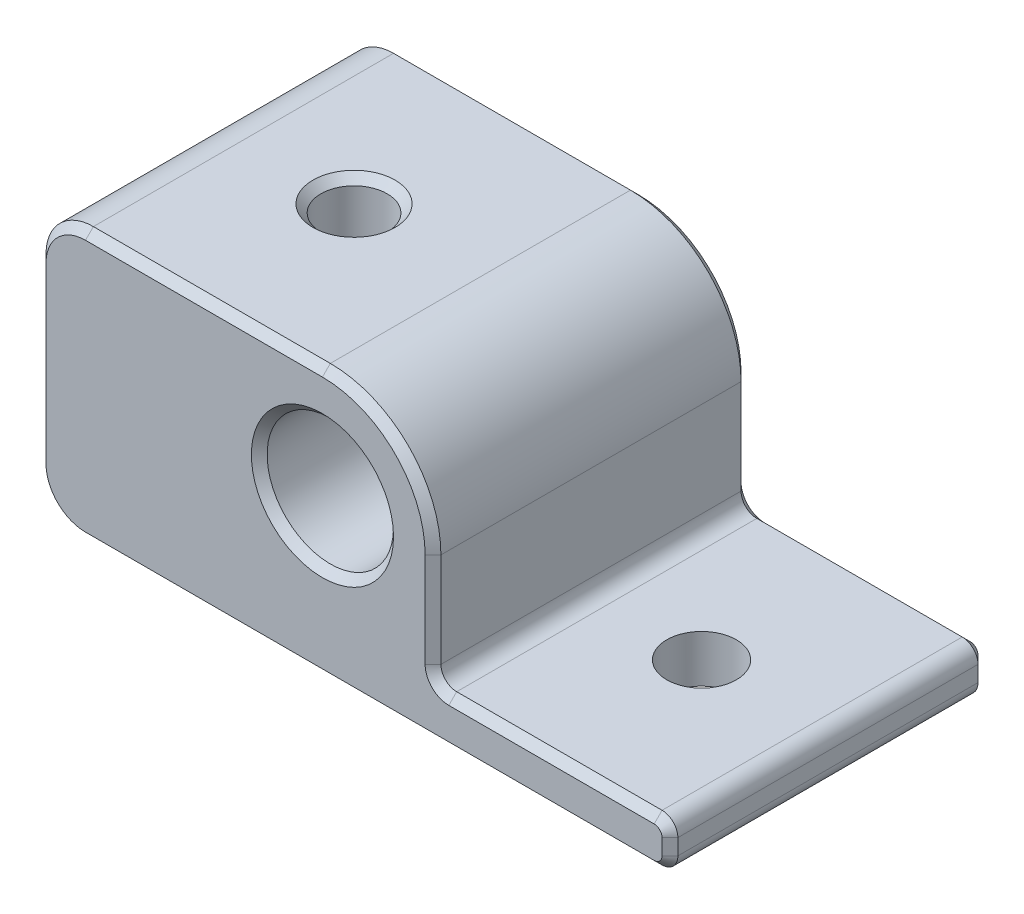
SolidWorks part; units mm, degrees
ref_plane "Front Plane" through (0, 0, 0) normal (0, 0, 1) x (1, 0, 0)
ref_plane "Top Plane" through (0, 0, 0) normal (0, 1, 0) x (1, 0, 0)
ref_plane "Right Plane" through (0, 0, 0) normal (1, 0, 0) x (0, 0, -1)
ref_plane "Plane1" through (0, -4.5711, 0) normal (0, -1, 0) x (1, 0, 0)
sketch "Sketch1" plane through (0, -4.5711, 0) normal (0, -1, 0) x (1, 0, 0)
  line L0 (19.5018, -0.4296) -> (59.5018, -0.4296)
  line L1 (59.5018, -0.4296) -> (59.5018, 19.5704)
  line L2 (59.5018, 19.5704) -> (19.5018, 19.5704)
  line L3 (19.5018, 19.5704) -> (19.5018, -0.4296)
extrude "Boss-Extrude1" add sketch "Sketch1" against normal blind 17
sketch "Sketch2" plane through (0, 0, 19.5704) normal (0, 0, 1) x (1, 0, 0)
  line L0 (44.5018, 12.4289) -> (44.5018, -1.5711)
  line L1 (44.5018, -1.5711) -> (59.5018, -1.5711)
  line L2 (59.5018, -1.5711) -> (59.5018, 12.4289)
  line L3 (59.5018, 12.4289) -> (44.5018, 12.4289)
extrude "Cut-Extrude1" cut sketch "Sketch2" against normal through all
hole_wizard "Ø4.4 (4.4) Diameter Hole1" positions "Sketch4" profile "Sketch3" hole size "Ø4.4" standard "ANSI Metric"
sketch "Sketch4" plane through (0, -4.5711, 0) normal (0, -1, 0) x (-1, 0, 0)
  point P0 (-51.5018, -9.5704)
sketch "Sketch3" plane through (51.5018, -4.5711, 9.5704) normal (1, 0, 0) x (0, 0, -1)
  line L0 (0, 0) -> (0, 17)
  line L1 (0, 17) -> (2.2, 17)
  line L2 (2.2, 17) -> (2.2, 0)
  line L5 (2.2, 0) -> (0, 0)
  line L11 (0, -6.35) -> (0, 107.95) construction
  dimension "Thru Hole Dia." = 4.4
  dimension "Thru Hole Depth" = 17
hole_wizard "Ø4.2 (4.2) Diameter Hole1" positions "Sketch6" profile "Sketch5" hole size "Ø4.2" standard "ANSI Metric"
sketch "Sketch6" plane through (0, 12.4289, 0) normal (0, 1, 0) x (1, 0, 0)
  point P0 (29.5018, -9.5704)
sketch "Sketch5" plane through (29.5018, 12.4289, 9.5704) normal (1, 0, 0) x (0, 0, 1)
  line L0 (0, 0) -> (0, 17)
  line L1 (0, 17) -> (2.1, 17)
  line L2 (2.1, 17) -> (2.1, 0)
  line L5 (2.1, 0) -> (0, 0)
  line L11 (0, -6.35) -> (0, 107.95) construction
  dimension "Thru Hole Dia." = 4.2
  dimension "Thru Hole Depth" = 17
hole_wizard "Hole1" positions "Sketch8" profile "Sketch7" legacy
sketch "Sketch8" plane through (0, 0, 19.5704) normal (0, 0, 1) x (1, 0, 0)
  point P0 (37.5018, 5.4289)
sketch "Sketch7" plane through (37.5018, 5.4289, 19.5704) normal (1, 0, 0) x (0, -1, 0)
  line L0 (0, 0) -> (0, 20)
  line L1 (0, 20) -> (3, 20)
  line L2 (3, 20) -> (3, 19)
  line L3 (3, 19) -> (4, 18)
  line L4 (4, 18) -> (4, 0)
  line L5 (4, 0) -> (0, 0)
  line L6 (0, -6.13) -> (0, 109.2824) construction
  line L7 (-3, 19) -> (-4, 18) construction
  line L8 (0, 20) -> (-3, 20) construction
  dimension "Diameter" = 6
  dimension "Depth" = 20
  dimension "C-Drill Diameter" = 8
  dimension "C-Drill Depth" = 18
  dimension "C-Drill Angle" = 90
fillet "Fillet1" radius 1 3 edges at (44.5018, -1.5711, 9.5704) (59.5018, -1.5711, 9.5704) (59.5018, -4.5711, 9.5704)
fillet "Fillet2" radius 3 2 edges at (19.5018, -4.5711, 9.5704) (19.5018, 12.4289, 9.5704)
fillet "Fillet3" radius 7 1 edges at (44.5018, 12.4289, 9.5704)
chamfer "Chamfer1" distance 0.5 angle 45 27 edges at (40.5018, -4.5711, 19.5704) (59.2089, -4.2782, 19.5704) (20.3804, -3.6924, 19.5704) (59.5018, -3.0711, 19.5704) (19.5018, 3.9289, 19.5704) (59.2089, -1.864, 19.5704) (20.3804, 11.5503, 19.5704) (52.0018, -1.5711, 19.5704) (30.0018, 12.4289, 19.5704) (44.7946, -1.2782, 19.5704) (42.4515, 10.3787, 19.5704) (44.5018, 2.4289, 19.5704) (59.5018, -3.0711, -0.4296) (59.2089, -1.864, -0.4296) (59.2089, -4.2782, -0.4296) (52.0018, -1.5711, -0.4296) (40.5018, -4.5711, -0.4296) (44.7946, -1.2782, -0.4296) (20.3804, -3.6924, -0.4296) (44.5018, 2.4289, -0.4296) (19.5018, 3.9289, -0.4296) (42.4515, 10.3787, -0.4296) (20.3804, 11.5503, -0.4296) (30.0018, 12.4289, -0.4296) (29.5018, -4.5711, 11.6704) (41.5018, 5.4289, 19.5704) (29.5018, 12.4289, 11.6704)
